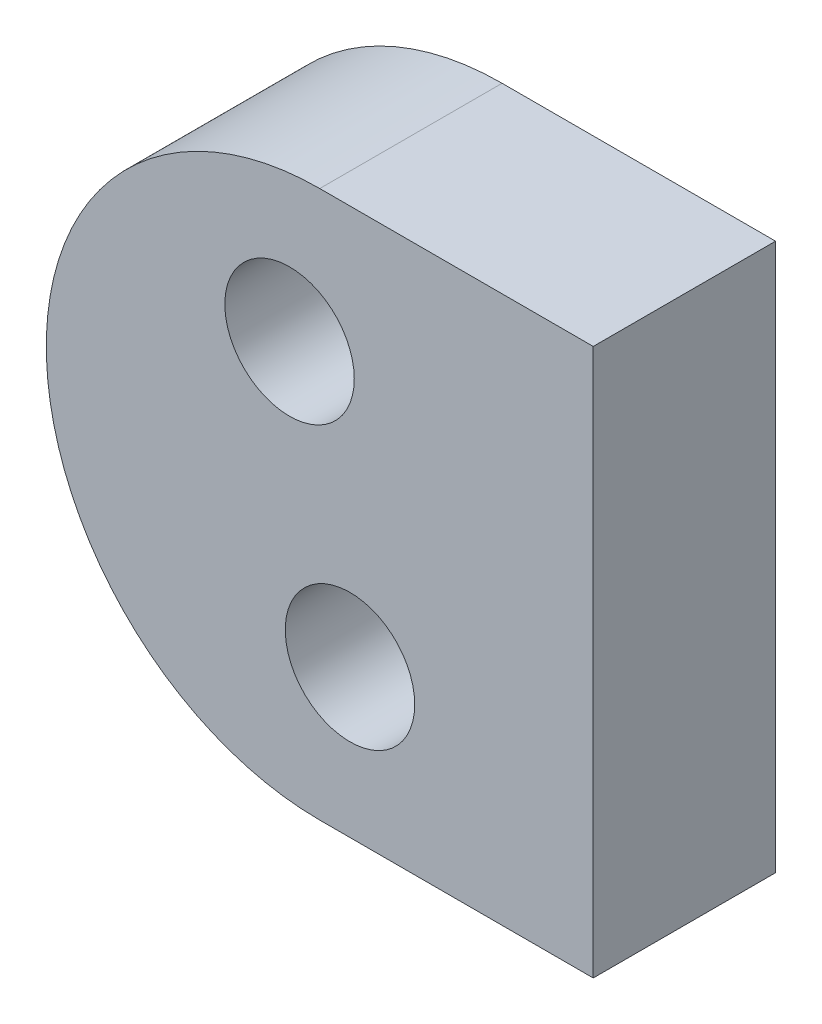
SolidWorks part; units mm, degrees
ref_plane "Front Plane" through (0, 0, 0) normal (0, 0, 1) x (1, 0, 0)
ref_plane "Top Plane" through (0, 0, 0) normal (0, 1, 0) x (1, 0, 0)
ref_plane "Right Plane" through (0, 0, 0) normal (1, 0, 0) x (0, 0, -1)
sketch "Sketch1" plane through (0, 0, 0) normal (0, 0, 1) x (1, 0, 0)
  line L0 (0, 0) -> (0.8287, -3.4519) construction
  line L1 (0, 0) -> (0, -3.55) construction
  line L3 (0.4144, 2.024) -> (4.1644, 2.024)
  line L5 (0.4144, -5.476) -> (4.1644, -5.476)
  line L6 (4.1644, 2.024) -> (4.1644, -5.476)
  circle A0 centre (0, 0) radius 0.8875
  circle A1 centre (0.8287, -3.4519) radius 0.8875
  arc A2 (0.4144, 2.024) -> (0.4144, -5.476) centre (0.4144, -1.726) ccw
  dimension "D1" = 1.775
  dimension "D4" = 7.5
  dimension "D2" = 13.5
  dimension "D3" = 3.55
extrude "Boss-Extrude1" add sketch "Sketch1" along normal blind 2.5
equation "\"filamentDia\"= 1.775"
equation "\"D1@Sketch1\"=\"filamentDia\""
equation "\"D3@Sketch1\"=\"filamentDia\"*2"
